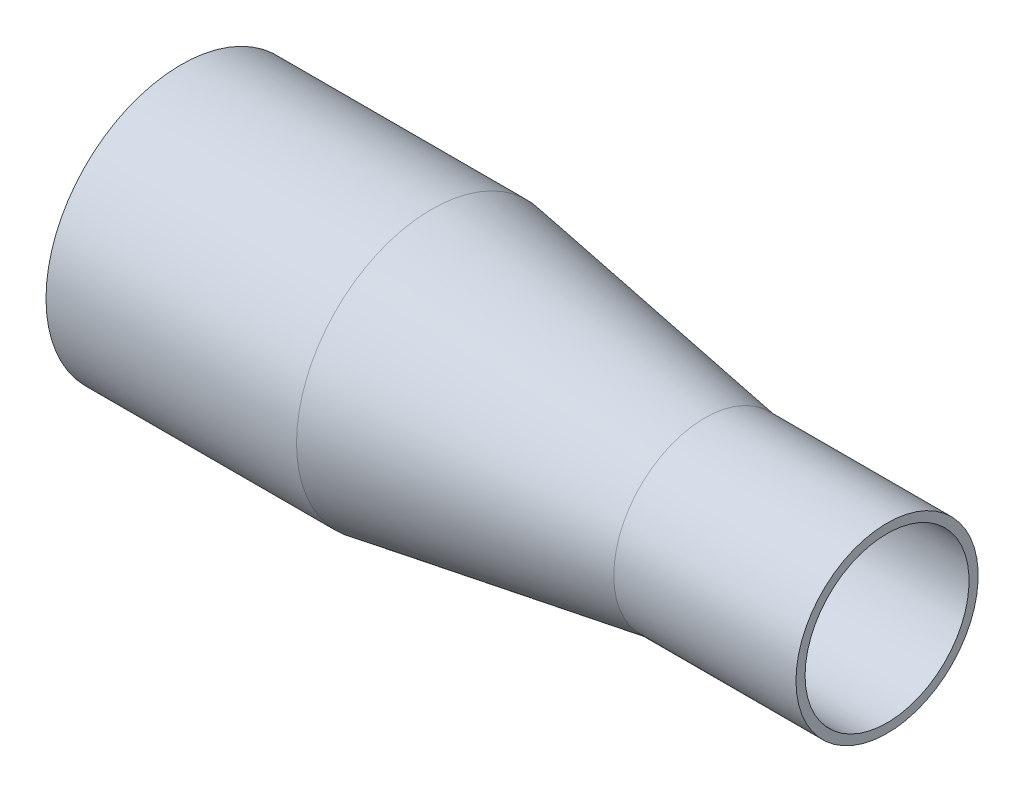
SolidWorks part; units mm, degrees
ref_plane "Front Plane" through (0, 0, 0) normal (0, 0, 1) x (1, 0, 0)
ref_plane "Top Plane" through (0, 0, 0) normal (0, 1, 0) x (1, 0, 0)
ref_plane "Right Plane" through (0, 0, 0) normal (1, 0, 0) x (0, 0, -1)
sketch "Sketch1" plane through (0, 0, 0) normal (0, 1, 0) x (1, 0, 0)
  line L0 (0, 0) -> (0, 37.6555)
  line L1 (0, 37.6555) -> (69.85, 37.6555)
  line L2 (69.85, 37.6555) -> (146.05, 25.4)
  line L3 (146.05, 25.4) -> (146.05, 0) construction
  line L4 (146.05, 25.4) -> (196.85, 25.4)
  line L5 (0, 0) -> (196.85, 0)
  line L6 (196.85, 25.4) -> (196.85, 0)
  line L7 (69.85, 37.6555) -> (69.85, 25.4) construction
  line L8 (69.85, 25.4) -> (146.05, 25.4) construction
  point P8 (194.8994, 0)
  dimension "D1" = 69.85
  dimension "D2" = 37.6555
  dimension "D3" = 25.4
  dimension "D4" = 50.8
  dimension "D5" = 76.2
revolve "Revolve1" add sketch "Sketch1" angle 360 about L5
shell "Shell1" thickness 2.54
